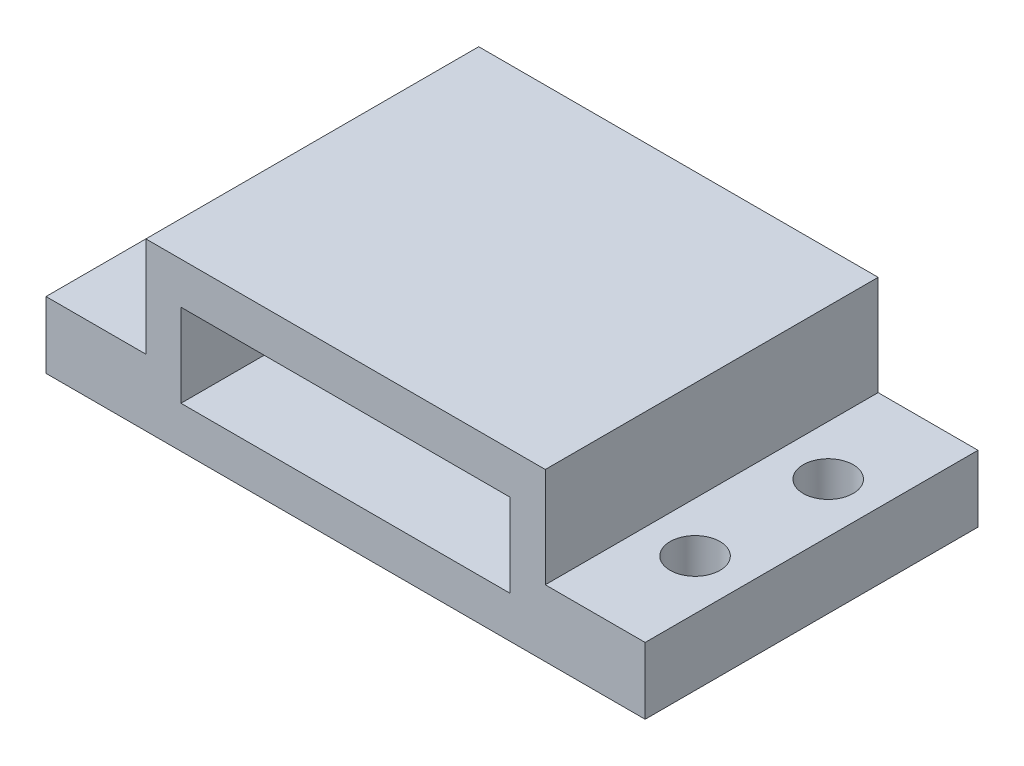
SolidWorks part; units mm, degrees
ref_plane "Front Plane" through (0, 0, 0) normal (0, 0, 1) x (1, 0, 0)
ref_plane "Top Plane" through (0, 0, 0) normal (0, 1, 0) x (1, 0, 0)
ref_plane "Right Plane" through (0, 0, 0) normal (1, 0, 0) x (0, 0, -1)
sketch "Sketch2" plane through (0, 0, 0) normal (0, 1, 0) x (1, 0, 0)
  line L0 (-6, 0) -> (6, 0)
  line L1 (-55, 0) -> (55, 0) construction
  line L2 (6, 0) -> (6, 10)
  line L3 (6, 10) -> (-6, 10)
  line L4 (0, -55) -> (0, 55) construction
  line L5 (0, 10) -> (0, 0)
  line L6 (-6, 0) -> (-6, 10)
extrude "Boss-Extrude2" add sketch "Sketch2" along normal blind 5 contours L6 L0 L5 L3 | L3 L5 L0 L2
sketch "Sketch4" plane through (0, 0, 0) normal (0, 0, 1) x (1, 0, 0)
  line L0 (-4.945, 1.25) -> (4.945, 1.25)
  line L1 (0, -2.7501) -> (0, 2.7501) construction
  line L2 (4.945, 1.25) -> (4.945, 3.75)
  line L3 (4.945, 3.75) -> (-4.945, 3.75)
  line L4 (0, 3.75) -> (0, 1.25)
  line L5 (-4.945, 1.25) -> (-4.945, 3.75)
  line L6 (0, 1.25) -> (0, 0)
extrude "Cut-Extrude1" cut sketch "Sketch4" against normal blind 8 contours L5 L0 L4 L3 | L3 L4 L0 L2
sketch "Sketch6" plane through (0, 0, -10) normal (0, 0, -1) x (-1, 0, 0)
  line L0 (-3.25, 2.25) -> (3.25, 2.25)
  line L1 (0, 2.7501) -> (0, -2.7501) construction
  line L2 (3.25, 2.25) -> (3.25, 2.75)
  line L3 (3.25, 2.75) -> (-3.25, 2.75)
  line L4 (0, 2.75) -> (0, 2.25)
  line L5 (0, 2.25) -> (0, 0) construction
  line L6 (-3.25, 2.25) -> (-3.25, 2.75)
  point P6 (0, 2.8523)
extrude "Cut-Extrude2" cut sketch "Sketch6" against normal blind 8 contours L6 L0 L4 L3 | L3 L4 L0 L2
sketch "Sketch7" plane through (-6, 0, 0) normal (-1, 0, 0) x (0, 0, 1)
  line L0 (-10, 0) -> (-10, 2)
  line L1 (5.5, 0) -> (-5.5, 0) construction
  line L2 (-10, 5) -> (-10, 0) construction
  line L3 (-10, 2) -> (0, 2)
  line L4 (0, -2.7501) -> (0, 2.7501) construction
  line L5 (0, 2) -> (0, 0)
  line L6 (-10, 0) -> (0, 0)
  point P6 (0, 0)
  point P12 (-10.2092, 0)
  point P13 (-10, 0)
extrude "Boss-Extrude3" add sketch "Sketch7" along normal blind 3
sketch "Sketch8" plane through (6, 0, 0) normal (1, 0, 0) x (0, 0, -1)
  line L0 (0, 0) -> (0, 2)
  line L1 (0, 2.7501) -> (0, -2.7501) construction
  line L2 (0, 2) -> (10, 2)
  line L4 (5.5, 0) -> (-5.5, 0) construction
  line L5 (10, 5) -> (10, 0) construction
  line L6 (10, 0) -> (0, 0)
  line L7 (10, 2) -> (10, 0)
extrude "Boss-Extrude4" add sketch "Sketch8" along normal blind 3
sketch "Sketch11" plane through (0, 2, 0) normal (0, 1, 0) x (1, 0, 0)
  line L0 (-7.5, 10) -> (-7.5, 0) construction
  line L1 (-9, 10) -> (-6, 10) construction
  line L2 (-2.7501, 0) -> (2.7501, 0) construction
  line L3 (-7.5, 10) -> (-7.5, 7) construction
  line L4 (-9, 5) -> (9, 5) construction
  line L5 (-9, 0) -> (-9, 10) construction
  line L6 (9, 10) -> (9, 0) construction
  line L7 (0, -2.7501) -> (0, 2.7501) construction
  circle A0 centre (-7.5, 7) radius 0.75
  circle A1 centre (-7.5, 3) radius 0.75
  circle A2 centre (7.5, 3) radius 0.75
  circle A3 centre (7.5, 7) radius 0.75
extrude "Cut-Extrude7" cut sketch "Sketch11" against normal blind 3
